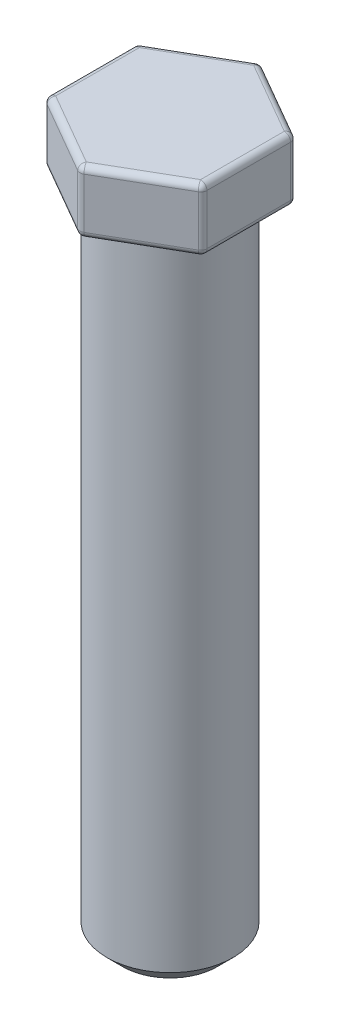
SolidWorks part; units mm, degrees
ref_plane "Front Plane" through (0, 0, 0) normal (0, 0, 1) x (1, 0, 0)
ref_plane "Top Plane" through (0, 0, 0) normal (0, 1, 0) x (1, 0, 0)
ref_plane "Right Plane" through (0, 0, 0) normal (1, 0, 0) x (0, 0, -1)
sketch "Sketch1" plane through (0, 0, 0) normal (0, 1, 0) x (1, 0, 0)
  circle A0 centre (0, 0) radius 2
  dimension "D1" = 4
extrude "Boss-Extrude1" add sketch "Sketch1" along normal blind 20.7
sketch "Sketch2" plane through (0, 20.7, 0) normal (0, 1, 0) x (1, 0, 0)
  line L1 (2.5, -1.4434) -> (2.5, 1.4434)
  line L2 (2.5, 1.4434) -> (0, 2.8868)
  line L3 (0, 2.8868) -> (-2.5, 1.4434)
  line L4 (-2.5, 1.4434) -> (-2.5, -1.4434)
  line L5 (-2.5, -1.4434) -> (0, -2.8868)
  line L6 (0, -2.8868) -> (2.5, -1.4434)
  circle A0 centre (0, 0) radius 2.5 construction
  point P1 (0, 0)
  dimension "D1" = 5
extrude "Boss-Extrude2" add sketch "Sketch2" along normal blind 2
chamfer "Chamfer1" distance 0.5 angle 45 1 edges at (0, 0, 2)
fillet "Fillet1" radius 0.2 19 edges at (-1.25, 22.7, 2.1651) (-2.5, 22.7, 0) (-1.25, 22.7, -2.1651) (1.25, 22.7, -2.1651) (2.5, 22.7, 0) (1.25, 22.7, 2.1651) (2.5, 20.7, 0) (1.25, 20.7, -2.1651) (-1.25, 20.7, -2.1651) (-2.5, 20.7, 0) (-1.25, 20.7, 2.1651) (1.25, 20.7, 2.1651) (0, 20.7, 2) (2.5, 21.7, 1.4434) (2.5, 21.7, -1.4434) (-2.5, 21.7, -1.4434) (-2.5, 21.7, 1.4434) (0, 21.7, 2.8868) (0, 21.7, -2.8868)
